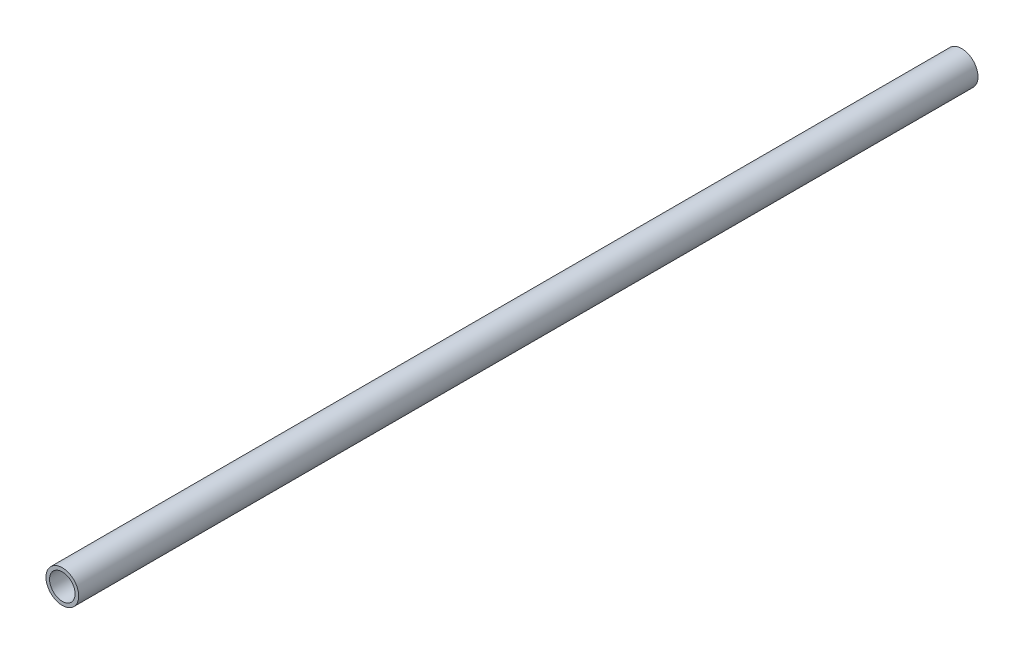
SolidWorks part; units mm, degrees
ref_plane "Front Plane" through (0, 0, 0) normal (0, 0, 1) x (1, 0, 0)
ref_plane "Top Plane" through (0, 0, 0) normal (0, 1, 0) x (1, 0, 0)
ref_plane "Right Plane" through (0, 0, 0) normal (1, 0, 0) x (0, 0, -1)
sketch "Sketch1" plane through (0, 0, 0) normal (0, 0, 1) x (1, 0, 0)
  circle A0 centre (0, 0) radius 4
  dimension "D1" = 8
extrude "Boss-Extrude1" add sketch "Sketch1" along normal blind 220
sketch "Sketch2" plane through (0, 0, 220) normal (0, 0, 1) x (1, 0, 0)
  circle A0 centre (0, 0) radius 3.125
  dimension "D1" = 6.25
extrude "Cut-Extrude1" cut sketch "Sketch2" against normal blind 6.5
ref_plane "Plane1" through (0, 0, 110) normal (0, 0, 1) x (1, 0, 0)
mirror "Mirror1" about plane through (0, 0, 110) normal (0, 0, 1) of "Cut-Extrude1"
